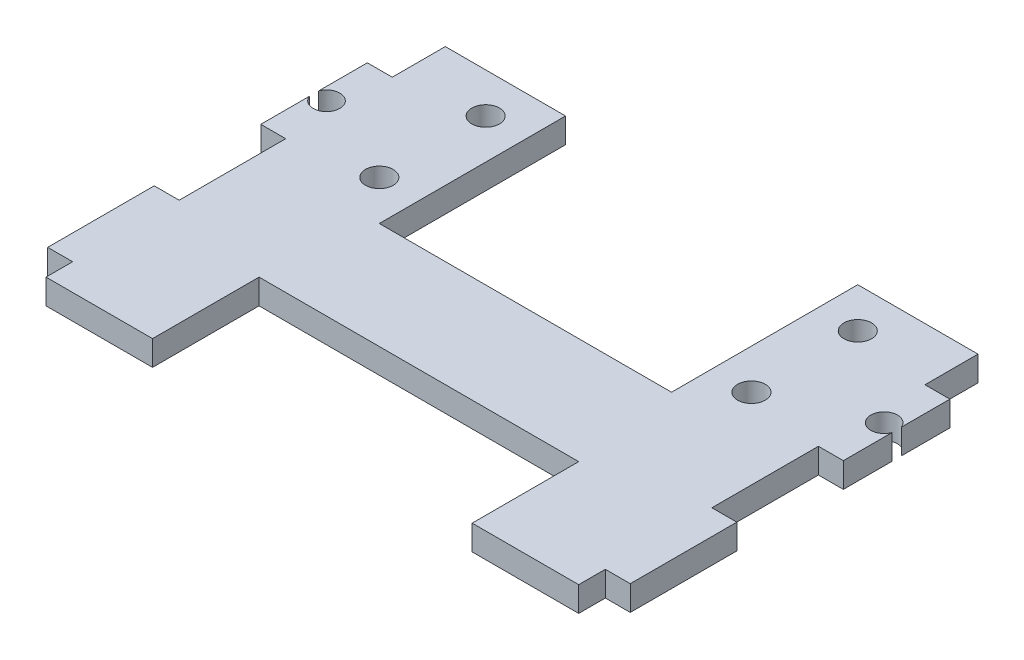
SolidWorks part; units mm, degrees
ref_plane "Front Plane" through (0, 0, 0) normal (0, 0, 1) x (1, 0, 0)
ref_plane "Top Plane" through (0, 0, 0) normal (0, 1, 0) x (1, 0, 0)
ref_plane "Right Plane" through (0, 0, 0) normal (1, 0, 0) x (0, 0, -1)
sketch "Sketch1" plane through (0, 0, 0) normal (0, 1, 0) x (1, 0, 0)
  line L0 (0, -55) -> (0, 55) construction
  line L5 (-31.75, 11.0996) -> (-17.4173, 11.0996)
  line L6 (-31.75, 11.0996) -> (-31.75, -11.0996)
  line L7 (-31.75, -11.0996) -> (-17.4173, -11.0996)
  line L8 (-17.4173, 11.0996) -> (-17.4173, -11.0996)
  line L9 (-31.75, -11.0996) -> (31.75, -11.0996)
  line L10 (-31.75, -11.0996) -> (-31.75, -36.4996)
  line L11 (-31.75, -36.4996) -> (31.75, -36.4996)
  line L12 (31.75, -11.0996) -> (31.75, -36.4996)
  line L13 (31.75, -11.0996) -> (17.4173, -11.0996)
  line L14 (17.4173, 11.0996) -> (17.4173, -11.0996)
  line L15 (31.75, 11.0996) -> (17.4173, 11.0996)
  line L16 (31.75, 11.0996) -> (31.75, -11.0996)
  line L17 (31.75, -33.3246) -> (34.7218, -33.3246)
  line L18 (-31.75, -20.6246) -> (-34.7218, -20.6246)
  line L19 (-31.75, -20.6246) -> (-31.75, -33.3246)
  line L20 (-31.75, -33.3246) -> (-34.7218, -33.3246)
  line L21 (-34.7218, -20.6246) -> (-34.7218, -33.3246)
  line L22 (34.7218, -20.6246) -> (34.7218, -33.3246)
  line L23 (31.75, -20.6246) -> (34.7218, -20.6246)
  line L24 (31.75, -20.6246) -> (31.75, -33.3246)
  line L25 (31.75, 4.7754) -> (34.7218, 4.7754)
  line L26 (-19.05, -36.4996) -> (19.05, -36.4996)
  line L27 (-19.05, -36.4996) -> (-19.05, -23.7996)
  line L28 (-19.05, -23.7996) -> (19.05, -23.7996)
  line L29 (19.05, -36.4996) -> (19.05, -23.7996)
  line L30 (-31.75, -7.9246) -> (-34.7218, -7.9246)
  line L31 (-31.75, -7.9246) -> (-31.75, 4.7754)
  line L32 (-31.75, 4.7754) -> (-34.7218, 4.7754)
  line L33 (-34.7218, -7.9246) -> (-34.7218, 4.7754)
  line L34 (34.7218, -7.9246) -> (34.7218, 4.7754)
  line L35 (31.75, -7.9246) -> (34.7218, -7.9246)
  line L36 (31.75, -7.9246) -> (31.75, 4.7754)
  circle A0 centre (22.1798, -6.3371) radius 1.6476
  circle A1 centre (22.1798, 6.3371) radius 1.6476
  circle A2 centre (-22.1798, -6.3371) radius 1.6476
  circle A3 centre (-22.1798, 6.3371) radius 1.6476
  point P8 (0, 0)
  point P35 (0, -36.4996)
  point P36 (0, -23.7996)
  dimension "D1" = 4.7625
  dimension "D2" = 4.7625
  dimension "D3" = 4.7625
  dimension "D4" = 25.4
  dimension "D5" = 2.9718
  dimension "D6" = 3.175
  dimension "D7" = 12.7
  dimension "D8" = 63.5
  dimension "D9" = 38.1
  dimension "D10" = 12.7
  dimension "D11" = 12.7
  dimension "D12" = 12.7
extrude "Boss-Extrude1" add sketch "Sketch1" along normal blind 2.9718 contours L8 L5 L6 L7 A3 A2 | L12 L9 L7 L10 L11 | L16 L15 L14 L9 A1 A0 | L18 L21 L20 L6 | L23 L16 L17 L22 | L33 L30 L6 L32 | L16 L35 L34 L25
sketch "Sketch2" plane through (0, 2.9718, 0) normal (0, 1, 0) x (1, 0, 0)
  line L0 (-33.2359, 4.7754) -> (-33.2359, -7.9246) construction
  line L1 (-31.75, 4.7754) -> (-34.7218, 4.7754) construction
  line L2 (-31.75, -7.9246) -> (-34.7218, -7.9246) construction
  line L4 (31.75, 4.7754) -> (34.7218, 4.7754) construction
  line L5 (33.2359, 4.7754) -> (33.2359, -7.9246) construction
  line L6 (31.75, -7.9246) -> (34.7218, -7.9246) construction
  circle A0 centre (-33.2359, -1.5746) radius 1.5875
  circle A1 centre (33.2359, -1.5746) radius 1.5875
  dimension "D1" = 3.175
extrude "Cut-Extrude1" cut sketch "Sketch2" against normal through all
